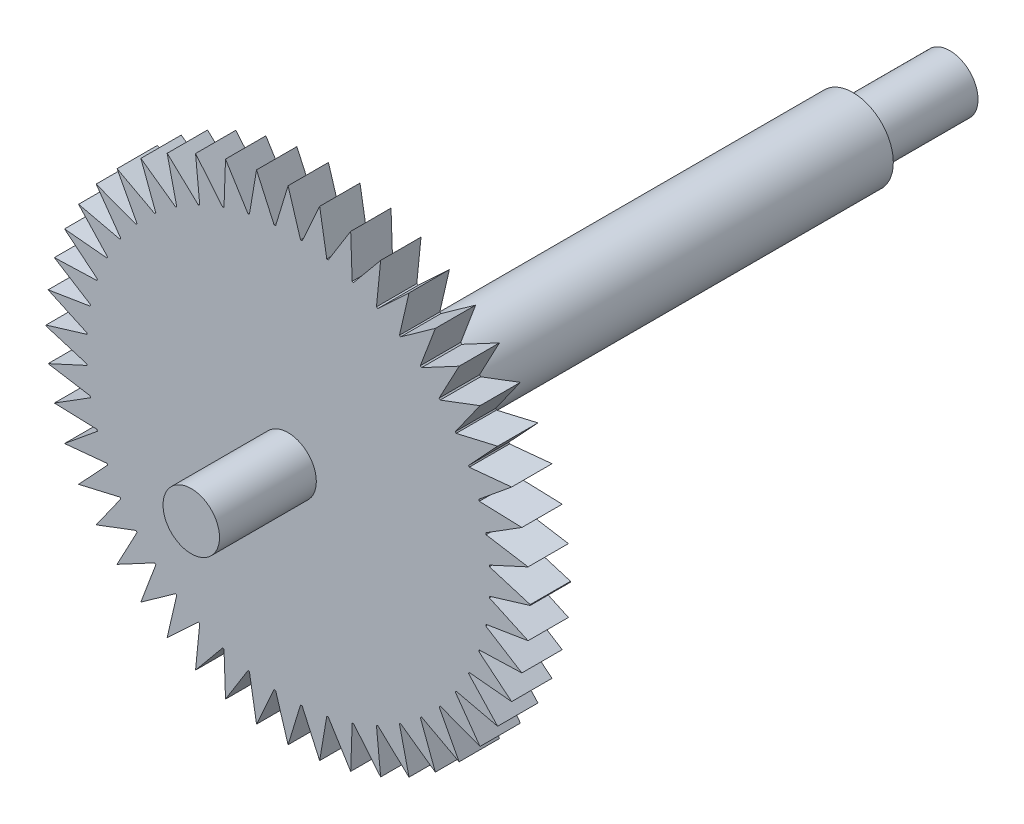
SolidWorks part; units mm, degrees
material "ABS"
ref_plane "Plan de face" through (0, 0, 0) normal (0, 0, 1) x (1, 0, 0)
ref_plane "Plan de dessus" through (0, 0, 0) normal (0, 1, 0) x (1, 0, 0)
ref_plane "Plan de droite" through (0, 0, 0) normal (1, 0, 0) x (0, 0, -1)
sketch "Esquisse1" plane through (0, 0, 0) normal (0, 0, 1) x (1, 0, 0)
  circle A0 centre (0, 0) radius 5
  dimension "D1" = 10
extrude "Boss.-Extru.1" add sketch "Esquisse1" along normal blind 70
sketch "Esquisse2" plane through (0, 0, 70) normal (0, 0, 1) x (1, 0, 0)
  circle A0 centre (0, 0) radius 30
  dimension "D1" = 60
extrude "Boss.-Extru.2" add sketch "Esquisse2" against normal blind 5
sketch "Esquisse3" plane through (0, 0, 0) normal (0, 0, -1) x (-1, 0, 0)
  circle A0 centre (0, 0) radius 3.5
  dimension "D1" = 7
extrude "Boss.-Extru.3" add sketch "Esquisse3" along normal blind 12
sketch "Esquisse4" plane through (0, 0, 70) normal (0, 0, 1) x (1, 0, 0)
  circle A0 centre (0, 0) radius 3.5
  dimension "D1" = 7
extrude "Boss.-Extru.4" add sketch "Esquisse4" along normal blind 12
sketch "Esquisse5" plane through (0, 0, 70) normal (0, 0, 1) x (1, 0, 0)
  line L0 (0, 30) -> (0, -30) construction
  line L1 (-30, 0) -> (30, 0) construction
  line L2 (0, 30) -> (-1.54, 24.9525)
  line L3 (0, 30) -> (1.54, 24.9525)
  line L4 (0, 0) -> (-3.9116, 29.7439) construction
  line L5 (0, 0) -> (-7.7565, 28.9799) construction
  line L6 (0, 0) -> (-11.4689, 27.7212) construction
  line L7 (0, 0) -> (-14.9855, 25.9892) construction
  line L8 (0, 0) -> (-18.2462, 23.8134) construction
  line L9 (0, 0) -> (-21.1954, 21.231) construction
  line L10 (0, 0) -> (-23.7827, 18.2861) construction
  line L11 (0, 0) -> (-25.964, 15.0291) construction
  line L12 (0, 0) -> (-27.7019, 11.5154) construction
  line L13 (0, 0) -> (-28.9669, 7.8051) construction
  line L14 (0, 0) -> (-29.7373, 3.9616) construction
  line L15 (-1.7396, 24.9394) -> (-3.9116, 29.7439)
  line L16 (-3.9116, 29.7439) -> (-4.7931, 24.5362)
  line L17 (-11.4689, 27.7212) -> (-8.104, 23.6501)
  line L18 (-10.9506, 22.4741) -> (-11.4689, 27.7212)
  line L19 (-14.9855, 25.9892) -> (-11.1301, 22.3858)
  line L20 (-14.9855, 25.9892) -> (-13.7983, 20.8472)
  line L21 (-7.7565, 28.9799) -> (-4.9638, 24.5023)
  line L22 (-7.7565, 28.9799) -> (-7.9391, 23.7059)
  line L23 (-21.1954, 21.231) -> (-16.5394, 18.7469)
  line L24 (-21.1954, 21.231) -> (-18.7191, 16.5709)
  line L25 (-18.8511, 16.4206) -> (-23.7827, 18.2861)
  line L26 (-23.7827, 18.2861) -> (-20.7272, 13.9779)
  line L27 (-25.964, 15.0291) -> (-20.8241, 13.8333)
  line L28 (-25.964, 15.0291) -> (-22.367, 11.1676)
  line L29 (-27.7019, 11.5154) -> (-22.4443, 11.0116)
  line L30 (-23.628, 8.1681) -> (-27.7019, 11.5154)
  line L31 (-28.9669, 7.8051) -> (-23.6926, 7.9789)
  line L32 (-28.9669, 7.8051) -> (-24.4939, 5.0049)
  line L33 (-18.2462, 23.8134) -> (-13.9431, 20.7507)
  line L34 (-16.3889, 18.8786) -> (-18.2462, 23.8134)
  line L35 (-30, 0.0504) -> (-24.9499, 1.5819)
  line L36 (-30, 0.0504) -> (-24.9551, -1.4981)
  line L37 (-24.5331, 4.8088) -> (-29.7373, 3.9616)
  line L38 (-29.7373, 3.9616) -> (-24.9383, 1.7556)
  line L39 (30, 0.0504) -> (24.9499, 1.5819)
  line L40 (29.7373, 3.9616) -> (24.9383, 1.7556)
  line L41 (24.5331, 4.8088) -> (29.7373, 3.9616)
  line L42 (28.9669, 7.8051) -> (24.4939, 5.0049)
  line L43 (28.9669, 7.8051) -> (23.6926, 7.9789)
  line L44 (23.628, 8.1681) -> (27.7019, 11.5154)
  line L45 (27.7019, 11.5154) -> (22.4443, 11.0116)
  line L46 (25.964, 15.0291) -> (22.367, 11.1676)
  line L47 (25.964, 15.0291) -> (20.8241, 13.8333)
  line L48 (23.7827, 18.2861) -> (20.7272, 13.9779)
  line L49 (18.8511, 16.4206) -> (23.7827, 18.2861)
  line L50 (21.1954, 21.231) -> (18.7191, 16.5709)
  line L51 (21.1954, 21.231) -> (16.5394, 18.7469)
  line L52 (16.3889, 18.8786) -> (18.2462, 23.8134)
  line L53 (18.2462, 23.8134) -> (13.9431, 20.7507)
  line L54 (14.9855, 25.9892) -> (13.7983, 20.8472)
  line L55 (14.9855, 25.9892) -> (11.1301, 22.3858)
  line L56 (10.9506, 22.4741) -> (11.4689, 27.7212)
  line L57 (11.4689, 27.7212) -> (8.104, 23.6501)
  line L58 (7.7565, 28.9799) -> (7.9391, 23.7059)
  line L59 (7.7565, 28.9799) -> (4.9638, 24.5023)
  line L60 (3.9116, 29.7439) -> (4.7931, 24.5362)
  line L61 (1.7396, 24.9394) -> (3.9116, 29.7439)
  line L62 (0, 30) -> (1.54, 24.9525)
  line L63 (30, -0.0504) -> (24.9499, -1.5819)
  line L64 (29.7373, -3.9616) -> (24.9383, -1.7556)
  line L65 (24.5331, -4.8088) -> (29.7373, -3.9616)
  line L66 (28.9669, -7.8051) -> (24.4939, -5.0049)
  line L67 (28.9669, -7.8051) -> (23.6926, -7.9789)
  line L68 (23.628, -8.1681) -> (27.7019, -11.5154)
  line L69 (27.7019, -11.5154) -> (22.4443, -11.0116)
  line L70 (25.964, -15.0291) -> (22.367, -11.1676)
  line L71 (25.964, -15.0291) -> (20.8241, -13.8333)
  line L72 (23.7827, -18.2861) -> (20.7272, -13.9779)
  line L73 (18.8511, -16.4206) -> (23.7827, -18.2861)
  line L74 (21.1954, -21.231) -> (18.7191, -16.5709)
  line L75 (21.1954, -21.231) -> (16.5394, -18.7469)
  line L76 (16.3889, -18.8786) -> (18.2462, -23.8134)
  line L77 (18.2462, -23.8134) -> (13.9431, -20.7507)
  line L78 (14.9855, -25.9892) -> (13.7983, -20.8472)
  line L79 (14.9855, -25.9892) -> (11.1301, -22.3858)
  line L80 (10.9506, -22.4741) -> (11.4689, -27.7212)
  line L81 (11.4689, -27.7212) -> (8.104, -23.6501)
  line L82 (7.7565, -28.9799) -> (7.9391, -23.7059)
  line L83 (7.7565, -28.9799) -> (4.9638, -24.5023)
  line L84 (3.9116, -29.7439) -> (4.7931, -24.5362)
  line L85 (1.7396, -24.9394) -> (3.9116, -29.7439)
  line L86 (0, -30) -> (1.54, -24.9525)
  line L87 (0, -30) -> (-1.54, -24.9525)
  line L88 (-1.7396, -24.9394) -> (-3.9116, -29.7439)
  line L89 (-3.9116, -29.7439) -> (-4.7931, -24.5362)
  line L90 (-7.7565, -28.9799) -> (-4.9638, -24.5023)
  line L91 (-7.7565, -28.9799) -> (-7.9391, -23.7059)
  line L92 (-11.4689, -27.7212) -> (-8.104, -23.6501)
  line L93 (-10.9506, -22.4741) -> (-11.4689, -27.7212)
  line L94 (-14.9855, -25.9892) -> (-11.1301, -22.3858)
  line L95 (-14.9855, -25.9892) -> (-13.7983, -20.8472)
  line L96 (-18.2462, -23.8134) -> (-13.9431, -20.7507)
  line L97 (-16.3889, -18.8786) -> (-18.2462, -23.8134)
  line L98 (-21.1954, -21.231) -> (-16.5394, -18.7469)
  line L99 (-21.1954, -21.231) -> (-18.7191, -16.5709)
  line L100 (-18.8511, -16.4206) -> (-23.7827, -18.2861)
  line L101 (-23.7827, -18.2861) -> (-20.7272, -13.9779)
  line L102 (-25.964, -15.0291) -> (-20.8241, -13.8333)
  line L103 (-25.964, -15.0291) -> (-22.367, -11.1676)
  line L104 (-27.7019, -11.5154) -> (-22.4443, -11.0116)
  line L105 (-23.628, -8.1681) -> (-27.7019, -11.5154)
  line L106 (-28.9669, -7.8051) -> (-23.6926, -7.9789)
  line L107 (-28.9669, -7.8051) -> (-24.4939, -5.0049)
  line L108 (-24.5331, -4.8088) -> (-29.7373, -3.9616)
  line L109 (-29.7373, -3.9616) -> (-24.9383, -1.7556)
  line L110 (-30, -0.0504) -> (-24.9499, -1.5819)
  circle A0 centre (0, 0) radius 30
  circle A1 centre (0, 0) radius 25
  circle M5 centre (0, 0) radius 30
  dimension "D2" = 50
  dimension "D13" = 3.92
  dimension "D14" = 3.08
  dimension "D15" = 3.08
  dimension "D17" = 0.2
extrude "Enlèv. mat.-Extru.1" cut sketch "Esquisse5" against normal blind 10 contours A1 L2 L15 M5 | A1 L16 L21 M5 | A1 L22 L17 M5 | A1 L18 L19 M5 | A1 L20 L33 M5 | A1 L34 L23 M5 | A1 L24 L25 M5 | A1 L26 L27 M5 | A1 L28 L29 M5 | A1 L30 L31 M5 | A1 L32 L37 M5 | A1 L38 L35 M5 | A1 L110 L109 M5 | A1 L108 L107 M5 | A1 L106 L105 M5 | A1 L104 L103 M5 | A1 L102 L101 M5 | A1 L100 L99 M5 | A1 L98 L97 M5 | A1 L96 L95 M5 | A1 L94 L93 M5 | A1 L92 L91 M5 | A1 L90 L89 M5 | A1 L88 L87 M5 | A1 L61 L3 M5 | A1 L59 L60 M5 | A1 L57 L58 M5 | A1 L55 L56 M5 | A1 L53 L54 M5 | A1 L51 L52 M5 | A1 L49 L50 M5 | A1 L47 L48 M5 | A1 L45 L46 M5 | A1 L43 L44 M5 | A1 L41 L42 M5 | A1 L39 L40 M5 | A1 L64 L63 M5 | A1 L66 L65 M5 | A1 L68 L67 M5 | A1 L70 L69 M5 | A1 L72 L71 M5 | A1 L74 L73 M5 | A1 L76 L75 M5 | A1 L78 L77 M5 | A1 L80 L79 M5 | A1 L82 L81 M5 | A1 L84 L83 M5 | A1 L86 L85 M5 | A0
